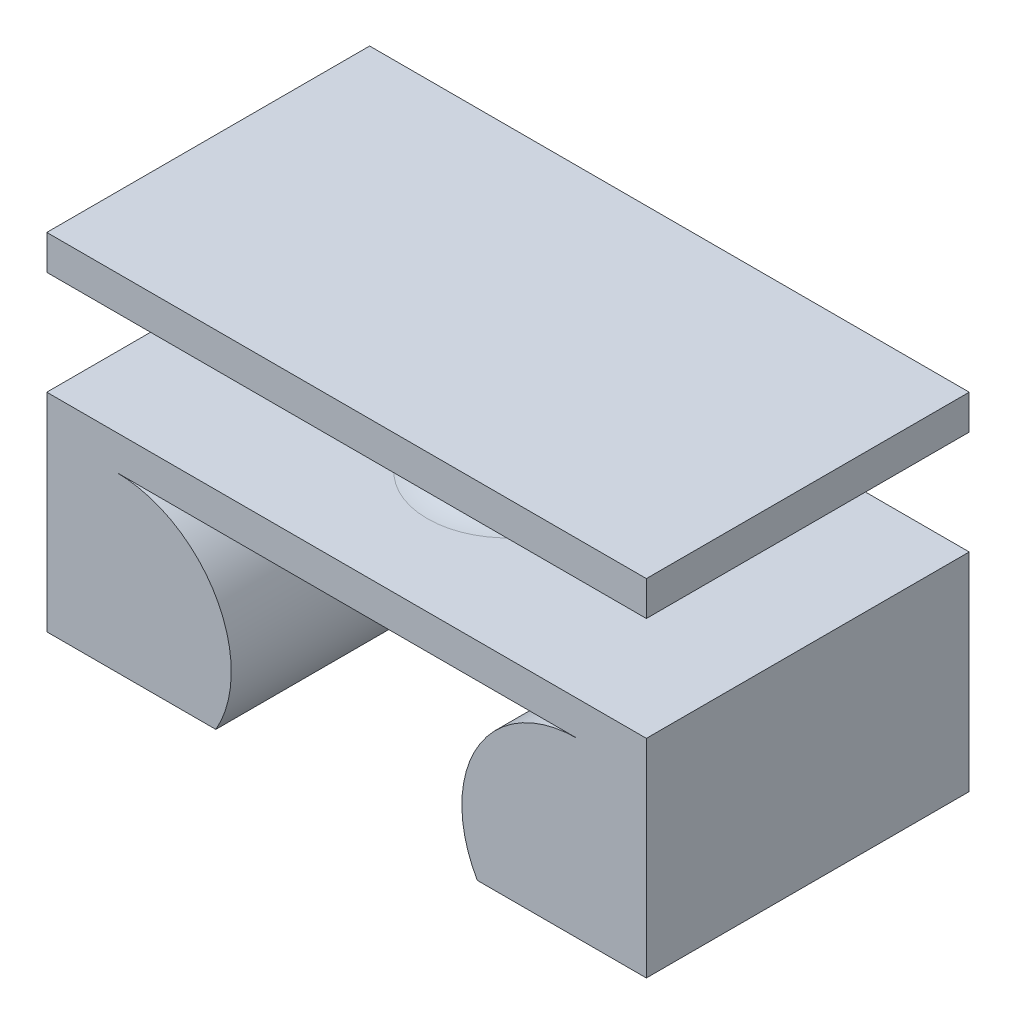
SolidWorks part; units mm, degrees
ref_plane "Front Plane" through (0, 0, 0) normal (0, 0, 1) x (1, 0, 0)
ref_plane "Top Plane" through (0, 0, 0) normal (0, 1, 0) x (1, 0, 0)
ref_plane "Right Plane" through (0, 0, 0) normal (1, 0, 0) x (0, 0, -1)
sketch "Sketch1" plane through (0, 0, 0) normal (0, 0, 1) x (1, 0, 0)
  line L0 (-5, 1.5) -> (5, 1.5)
  line L1 (6.5, 2.25) -> (-6.5, 2.25)
  line L2 (6.5, 2.25) -> (6.5, -2.25)
  line L3 (6.5, -2.25) -> (-6.5, -2.25)
  line L4 (-6.5, 2.25) -> (-6.5, -2.25)
  line L5 (6.5, 2.25) -> (-6.5, -2.25) construction
  line L6 (6.5, -2.25) -> (-6.5, 2.25) construction
  line L7 (0, 2.25) -> (0, -2.25) construction
  arc A0 (-5, -3.5) -> (-5, 1.5) centre (-5, -1) ccw
  arc A1 (5, -3.5) -> (5, 1.5) centre (5, -1) cw
  point P0 (0, 0)
  point P8 (0, 1.5)
  point P14 (0, 0)
  dimension "D5" = 2.5
  dimension "D1" = 13
  dimension "D2" = 4.5
  dimension "D3" = 10
  dimension "D4" = 0.75
extrude "Boss-Extrude1" add sketch "Sketch1" along normal mid plane 7 contours A1 L3 L2 L1 L4 A0 L0
sketch "Sketch2" plane through (0, 0, 0) normal (1, 0, 0) x (0, 0, -1)
  line L0 (5, 1.5) -> (-5, 1.5)
  line L1 (-3.5, 2.25) -> (3.5, 2.25) construction
  line L4 (3.5, 1.5) -> (3.5, 1)
  line L5 (2.8349, -2.25) -> (3.5, -2.25)
  line L6 (-3.5, -2.25) -> (3.5, -2.25) construction
  line L7 (3.5, -2.25) -> (3.5, 1)
  arc A0 (5, 1.5) -> (5, -3.5) centre (5, -1) ccw
  point P5 (0, 1.5)
  point P6 (0, 2.25)
  dimension "D3" = 2.5
  dimension "D1" = 0.75
  dimension "D2" = 10
extrude "Boss-Extrude2" add sketch "Sketch2" against normal mid plane 7 contours L7 A0 L5
sketch "Sketch3" plane through (0, 0, 0) normal (0, 0, 1) x (1, 0, 0)
  line L0 (6.5, 2.25) -> (-6.5, 2.25) construction
  line L1 (-1.75, 4.5) -> (1.75, 4.5)
  line L2 (0, 4.5) -> (0, 2.25)
  line L3 (-1.75, 2.25) -> (0, 2.25)
  line L4 (0, 5.875) -> (0, 0.875) construction
  arc A0 (-1.75, 2.25) -> (-1.75, 4.5) centre (-1.75, 3.375) ccw
  arc A1 (1.75, 4.5) -> (1.75, 2.25) centre (1.75, 3.375) ccw
  point P5 (0, 2.25)
  point P7 (0, 4.5)
  point P16 (0, 3.375)
  point P17 (0, 3.375)
  dimension "D1" = 1.125
  dimension "D2" = 3.5
  dimension "D3" = 5
revolve "Revolve1" add sketch "Sketch3" angle 360 about L4
sketch "Sketch4" plane through (0, 4.5, 0) normal (0, 1, 0) x (1, 0, 0)
  line L4 (6.5, 3.5) -> (-6.5, 3.5)
  line L5 (-6.5, 3.5) -> (-6.5, -3.5)
  line L6 (-6.5, -3.5) -> (6.5, -3.5)
  line L7 (6.5, -3.5) -> (6.5, 3.5)
  line L8 (6.5, 3.5) -> (-6.5, 3.5)
  line L9 (-6.5, 3.5) -> (-6.5, -3.5)
  line L10 (-6.5, -3.5) -> (6.5, -3.5)
  line L11 (6.5, -3.5) -> (6.5, 3.5)
  dimension "D1" = 0
extrude "Boss-Extrude3" add sketch "Sketch4" along normal blind 0.75
